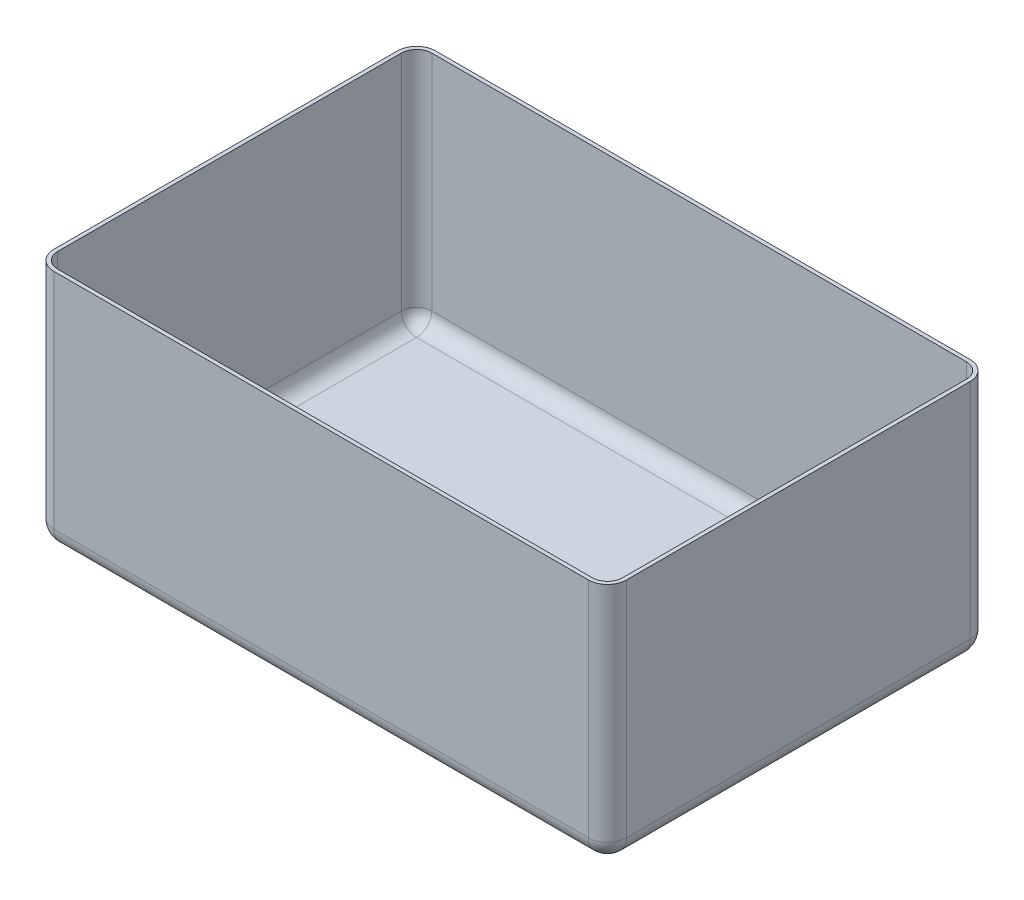
SolidWorks part; units mm, degrees
ref_plane "Front Plane" through (0, 0, 0) normal (0, 0, 1) x (1, 0, 0)
ref_plane "Top Plane" through (0, 0, 0) normal (0, 1, 0) x (1, 0, 0)
ref_plane "Right Plane" through (0, 0, 0) normal (1, 0, 0) x (0, 0, -1)
sketch "Sketch1" plane through (0, 0, 0) normal (0, 1, 0) x (1, 0, 0)
  line L1 (150, -100) -> (-150, -100)
  line L2 (150, -100) -> (150, 100)
  line L3 (150, 100) -> (-150, 100)
  line L4 (-150, -100) -> (-150, 100)
  line L5 (150, -100) -> (-150, 100) construction
  line L6 (150, 100) -> (-150, -100) construction
  point P0 (0, 0)
  dimension "D1" = 300
  dimension "D2" = 200
extrude "Boss-Extrude1" add sketch "Sketch1" along normal blind 127 contours L2 L1 L4 L3
fillet "Fillet1" radius 10 8 edges at (-150, 0, 0) (0, 0, 100) (150, 0, 0) (0, 0, -100) (150, 63.5, 100) (150, 63.5, -100) (-150, 63.5, -100) (-150, 63.5, 100)
shell "Shell1" thickness 2
